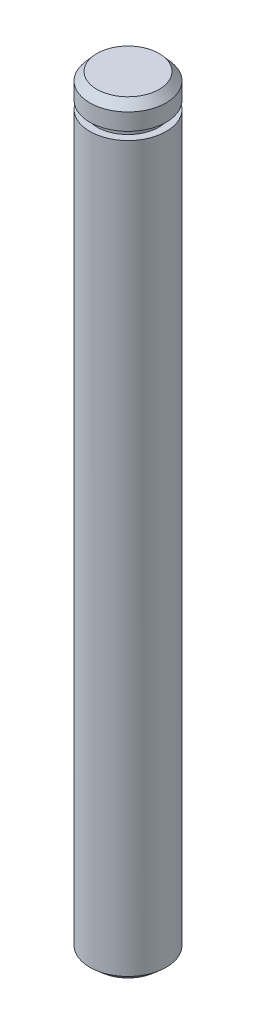
SolidWorks part; units mm, degrees
ref_plane "Front Plane" through (0, 0, 0) normal (0, 0, 1) x (1, 0, 0)
ref_plane "Top Plane" through (0, 0, 0) normal (0, 1, 0) x (1, 0, 0)
ref_plane "Right Plane" through (0, 0, 0) normal (1, 0, 0) x (0, 0, -1)
sketch "Sketch1" plane through (0, 0, 0) normal (0, 1, 0) x (1, 0, 0)
  circle A0 centre (0, 0) radius 4.7625
  dimension "D1" = 9.525
extrude "Boss-Extrude1" add sketch "Sketch1" along normal mid plane 95.25
chamfer "Chamfer1" distance 1.016 angle 41 2 edges at (0, -47.625, 4.7625) (0, 47.625, 4.7625)
sketch "Sketch3" plane through (0, 0, 0) normal (1, 0, 0) x (0, 0, -1)
  line L1 (4.7625, -46.7418) -> (4.7625, 46.609) construction
  line L2 (4.7625, -44.6458) -> (3.8481, -44.6458)
  line L3 (4.7625, -44.6458) -> (4.7625, -43.6552)
  line L4 (4.7625, -43.6552) -> (3.8481, -43.6552)
  line L5 (3.8481, -44.6458) -> (3.8481, -43.6552)
  line L6 (0, -47.8208) -> (0, -31.0338) construction
  line L7 (4.7625, -0.0664) -> (-4.7625, -0.0664) construction
  line L8 (-4.7625, 46.609) -> (-4.7625, -46.7418) construction
  line L9 (4.7625, 43.5224) -> (3.8481, 43.5224)
  line L10 (4.7625, 44.513) -> (4.7625, 43.5224)
  line L11 (4.7625, 44.513) -> (3.8481, 44.513)
  line L12 (3.8481, 44.513) -> (3.8481, 43.5224)
  dimension "D1" = 0.9906
  dimension "D2" = 7.6962
  dimension "D3" = 3.175
revolve "Cut-Revolve1" cut sketch "Sketch3" angle 360 about L6
